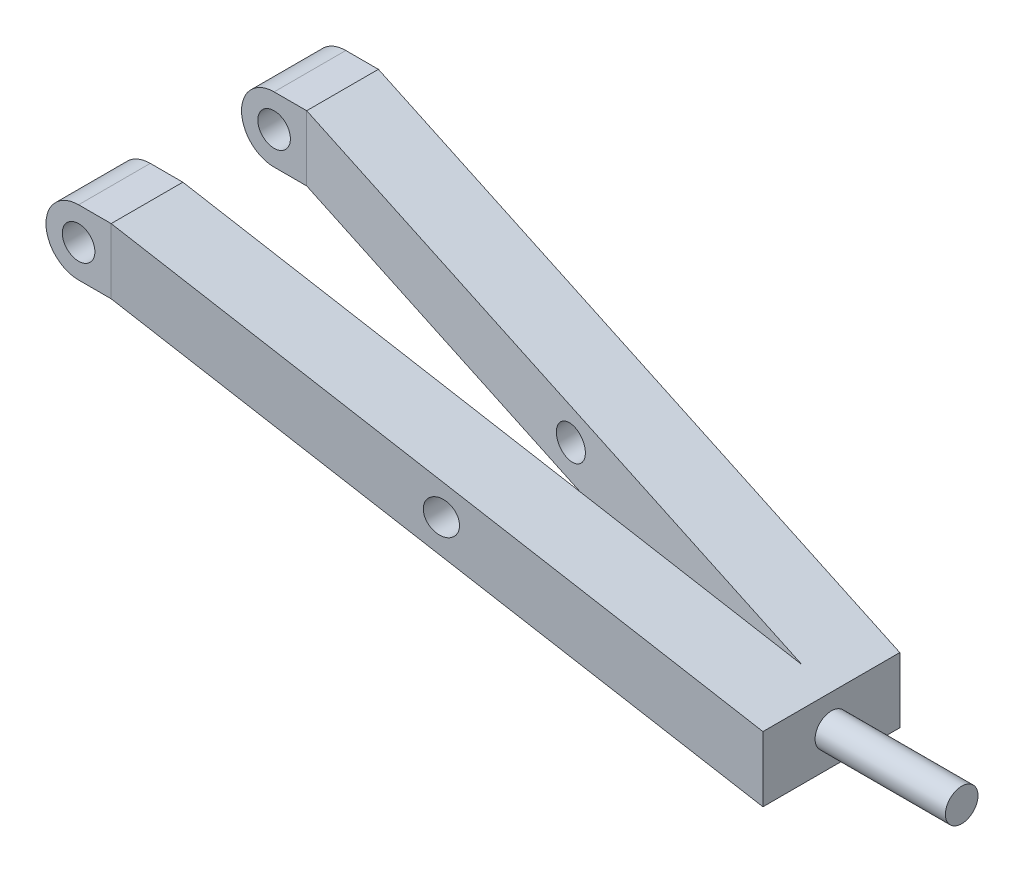
SolidWorks part; units mm, degrees
ref_plane "Front" through (0, 0, 0) normal (0, 0, 1) x (1, 0, 0)
ref_plane "Top" through (0, 0, 0) normal (0, 1, 0) x (1, 0, 0)
ref_plane "Right" through (0, 0, 0) normal (1, 0, 0) x (0, 0, -1)
sketch "Sketch1" plane through (0, 0, 0) normal (0, 1, 0) x (1, 0, 0)
  point P0 (12.7, -38.1)
  dimension "D1" = 38.1
  dimension "D2" = 12.7
ref_plane "Plane1" through (0, 0, 12.7) normal (0, 0, 1) x (1, 0, 0)
sketch "Sketch2" plane through (0, 0, 12.7) normal (0, 0, 1) x (1, 0, 0)
  point P0 (241.3, -69.85)
  dimension "D1" = 69.85
  dimension "D2" = 228.6
sketch3d "3DSketch4"
  line L0 (12.7, 0, 38.1) -> (241.3, -69.85, 12.7)
ref_plane "Plane3" through (12.7, 0, 0) normal (1, 0, 0) x (0, 0, -1)
sketch "Sketch10" plane through (12.7, 0, 0) normal (1, 0, 0) x (0, 0, -1)
  line L1 (-52.07, 12.7) -> (-24.13, 12.7)
  line L2 (-52.07, 12.7) -> (-52.07, -12.7)
  line L3 (-52.07, -12.7) -> (-24.13, -12.7)
  line L4 (-24.13, 12.7) -> (-24.13, -12.7)
  line L5 (-52.07, 12.7) -> (-24.13, -12.7) construction
  line L6 (-52.07, -12.7) -> (-24.13, 12.7) construction
  point P0 (-38.1, 0)
  dimension "D1" = 27.94
  dimension "D2" = 25.4
sweep "Sweep3" add profiles "Sketch10" path "3DSketch4"
sketch "Sketch12" plane through (12.7, 0, 0) normal (1, 0, 0) x (0, 0, -1)
  line L4 (-24.13, -12.7) -> (-24.13, 12.7)
  line L5 (-52.07, -12.7) -> (-24.13, -12.7)
  line L6 (-52.07, 12.7) -> (-52.07, -12.7)
  line L7 (-24.13, 12.7) -> (-52.07, 12.7)
  line L8 (-24.13, -12.7) -> (-24.13, 12.7)
  line L9 (-52.07, -12.7) -> (-24.13, -12.7)
  line L10 (-52.07, 12.7) -> (-52.07, -12.7)
  line L11 (-24.13, 12.7) -> (-52.07, 12.7)
  dimension "D1" = 0
extrude "Boss-Extrude2" add sketch "Sketch12" against normal blind 25.4
mirror "Mirror5" about plane through (0, 0, 0) normal (0, 0, 1) of "Boss-Extrude2", "Sweep3"
sketch "Sketch13" plane through (0, 0, -52.07) normal (0, 0, -1) x (-1, 0, 0)
  circle A0 centre (0, 0) radius 6.35
  dimension "D1" = 12.7
extrude "Cut-Extrude4" cut sketch "Sketch13" against normal through all
sketch "Sketch14" plane through (0, 0, -52.07) normal (0, 0, -1) x (-1, 0, 0)
  line L0 (12.7, 12.7) -> (-12.7, 12.7) construction
  line L1 (12.7, 12.7) -> (12.7, -12.7) construction
  line L2 (12.7, 12.7) -> (0, 12.7)
  line L3 (12.7, 12.7) -> (12.7, 0)
  arc A0 (12.7, 0) -> (0, 12.7) centre (0, 0) ccw
extrude "Cut-Extrude5" cut sketch "Sketch14" against normal through all
mirror "Mirror6" about plane through (0, 0, 0) normal (0, 1, 0) of "Cut-Extrude5"
sketch "Sketch15" plane through (241.3, 0, 0) normal (1, 0, 0) x (0, 0, -1)
  line L0 (26.67, -69.85) -> (-26.67, -69.85) construction
  line L1 (26.67, -57.15) -> (26.67, -82.55) construction
  line L2 (-26.67, -57.15) -> (-26.67, -82.55) construction
  circle A0 centre (0, -69.85) radius 6.35
  dimension "D1" = 12.7
extrude "Boss-Extrude3" add sketch "Sketch15" along normal blind 50.8
sketch "Sketch16" plane through (0, 0, 0) normal (0, 0, 1) x (1, 0, 0)
  line L0 (12.7, -50) -> (12.7, 50) construction
  circle A0 centre (128.524, -34.925) radius 6.35
  dimension "D2" = 12.7
  dimension "D1" = 115.824
  dimension "D3" = 34.925
extrude "Cut-Extrude6" cut sketch "Sketch16" against normal through all and the other way through all
